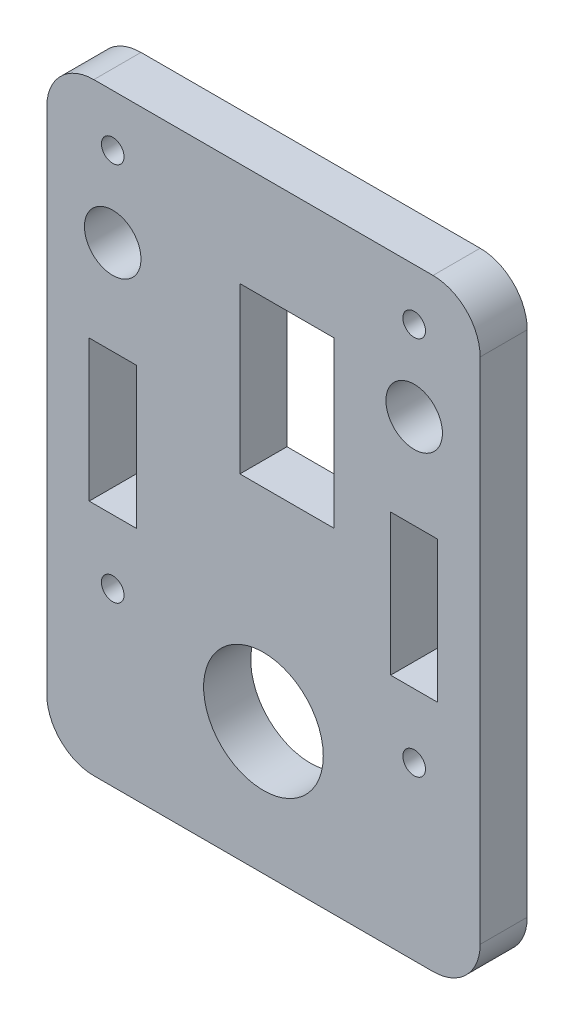
SolidWorks part; units mm, degrees
material "Acrylic (Medium-high impact)"
ref_plane "Front Plane" through (0, 0, 0) normal (0, 0, 1) x (1, 0, 0)
ref_plane "Top Plane" through (0, 0, 0) normal (0, 1, 0) x (1, 0, 0)
ref_plane "Right Plane" through (0, 0, 0) normal (1, 0, 0) x (0, 0, -1)
sketch "Sketch1" plane through (0, 0, 0) normal (0, 0, 1) x (1, 0, 0)
  line L0 (0, 0) -> (0, 64) construction
  line L1 (-23, 64) -> (23, 64)
  line L2 (23, 64) -> (23, 0)
  line L3 (23, 0) -> (-23, 0)
  line L5 (13.5, 40) -> (18.5, 40)
  line L6 (13.5, 40) -> (13.5, 25)
  line L7 (13.5, 25) -> (18.5, 25)
  line L8 (18.5, 40) -> (18.5, 25)
  line L9 (-2.5, 53) -> (7.5, 53)
  line L10 (-2.5, 53) -> (-2.5, 35.5)
  line L11 (-2.5, 35.5) -> (7.5, 35.5)
  line L12 (-18.5, 40) -> (-18.5, 25)
  line L13 (-13.5, 25) -> (-18.5, 25)
  line L14 (-13.5, 40) -> (-13.5, 25)
  line L15 (-13.5, 40) -> (-18.5, 40)
  line L16 (-23, 64) -> (-23, 0)
  line L17 (7.5, 53) -> (7.5, 35.5)
  circle A0 centre (16, 50) radius 3
  circle A1 centre (16, 18.2) radius 1.2
  circle A2 centre (16, 58.5) radius 1.2
  circle A3 centre (-16, 58.5) radius 1.2
  circle A4 centre (-16, 18.2) radius 1.2
  circle A5 centre (-16, 50) radius 3
  circle A6 centre (0, 14) radius 6.35
  point P18 (16, 40)
  point P34 (-16, 40)
  dimension "D2" = 2.4
  dimension "D4" = 6
  dimension "D16" = 12.7
  dimension "D1" = 15
  dimension "D5" = 5
  dimension "D6" = 16
  dimension "D7" = 14
  dimension "D8" = 10
  dimension "D9" = 25
  dimension "D10" = 18.2
  dimension "D11" = 5.5
  dimension "D12" = 17.5
  dimension "D13" = 3
  dimension "D14" = 10
  dimension "D15" = 23
  dimension "D17" = 36
  dimension "D18" = 6
extrude "Boss-Extrude1" add sketch "Sketch1" along normal blind 5
fillet "Fillet1" radius 5 4 edges at (-23, 0, 2.5) (23, 0, 2.5) (23, 64, 2.5) (-23, 64, 2.5)
